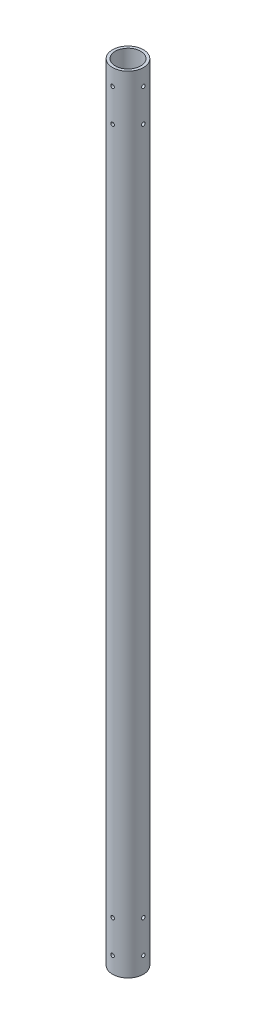
SolidWorks part; units mm, degrees
material "Carbon Fiber (2)"
ref_plane "Front Plane" through (0, 0, 0) normal (0, 0, 1) x (1, 0, 0)
ref_plane "Top Plane" through (0, 0, 0) normal (0, 1, 0) x (1, 0, 0)
ref_plane "Right Plane" through (0, 0, 0) normal (1, 0, 0) x (0, 0, -1)
sketch "Sketch1" plane through (0, 0, 0) normal (0, 1, 0) x (1, 0, 0)
  circle A0 centre (0, 0) radius 4.953
  circle A1 centre (0, 0) radius 5.9944
  dimension "D1" = 9.906
  dimension "D2" = 11.9888
extrude "Boss-Extrude1" add sketch "Sketch1" along normal blind 304.8
ref_plane "Plane1" through (0, 0, 5.9944) normal (0, 0, 1) x (1, 0, 0)
sketch "Sketch2" plane through (0, 0, 5.9944) normal (0, 0, 1) x (1, 0, 0)
  line L0 (0, 0) -> (0, 304.8) construction
  circle A0 centre (0, 6.35) radius 0.6985
  circle A1 centre (0, 19.05) radius 0.6985
  circle A2 centre (0, 298.45) radius 0.6985
  circle A3 centre (0, 285.75) radius 0.6985
  dimension "D2" = 1.397
  dimension "D3" = 1.397
  dimension "D6" = 1.397
  dimension "D9" = 1.397
  dimension "D1" = 304.8
  dimension "D4" = 6.35
  dimension "D5" = 12.7
  dimension "D7" = 6.35
  dimension "D8" = 12.7
extrude "Cut-Extrude1" cut sketch "Sketch2" against normal up to next
pattern_circular "CirPattern1" count 4 over 360 about axis through (0, 304.8, 0) along (0, 1, 0) of "Cut-Extrude1"
